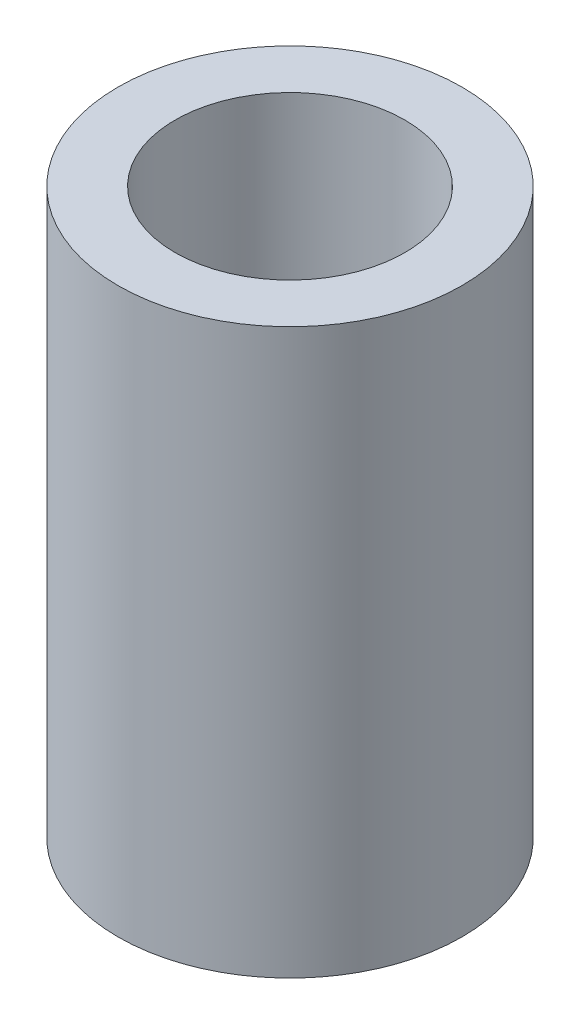
SolidWorks part; units mm, degrees
ref_plane "Front Plane" through (0, 0, 0) normal (0, 0, 1) x (1, 0, 0)
ref_plane "Top Plane" through (0, 0, 0) normal (0, 1, 0) x (1, 0, 0)
ref_plane "Right Plane" through (0, 0, 0) normal (1, 0, 0) x (0, 0, -1)
sketch "Sketch1" plane through (0, 0, 0) normal (0, 1, 0) x (1, 0, 0)
  circle A0 centre (0, 0) radius 25
  circle A1 centre (0, 0) radius 16.7
  dimension "D1" = 50
  dimension "D2" = 8.3
extrude "Boss-Extrude1" add sketch "Sketch1" along normal mid plane 82
